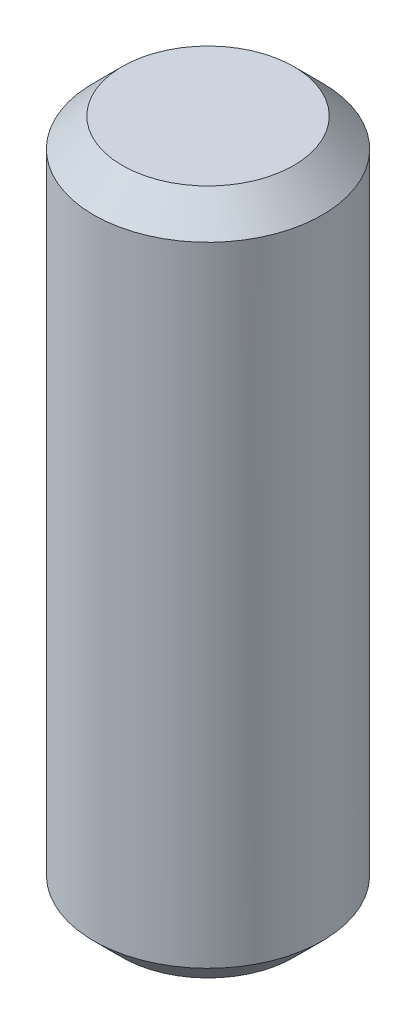
SolidWorks part; units mm, degrees
ref_plane "前基準面" through (0, 0, 0) normal (0, 0, 1) x (1, 0, 0)
ref_plane "上基準面" through (0, 0, 0) normal (0, 1, 0) x (1, 0, 0)
ref_plane "右基準面" through (0, 0, 0) normal (1, 0, 0) x (0, 0, -1)
sketch "草圖1" plane through (0, 0, 0) normal (0, 0, 1) x (1, 0, 0)
  line L1 (0, 0) -> (4, 0)
  line L2 (0, 0) -> (0, 24)
  line L3 (0, 24) -> (4, 24)
  line L4 (4, 0) -> (4, 24)
  dimension "D1" = 24
  dimension "D2" = 4
revolve "旋轉1" add sketch "草圖1" angle 360 about L2
chamfer "導角1" distance 1 angle 45 2 edges at (0, 0, -4) (0, 24, -4)
